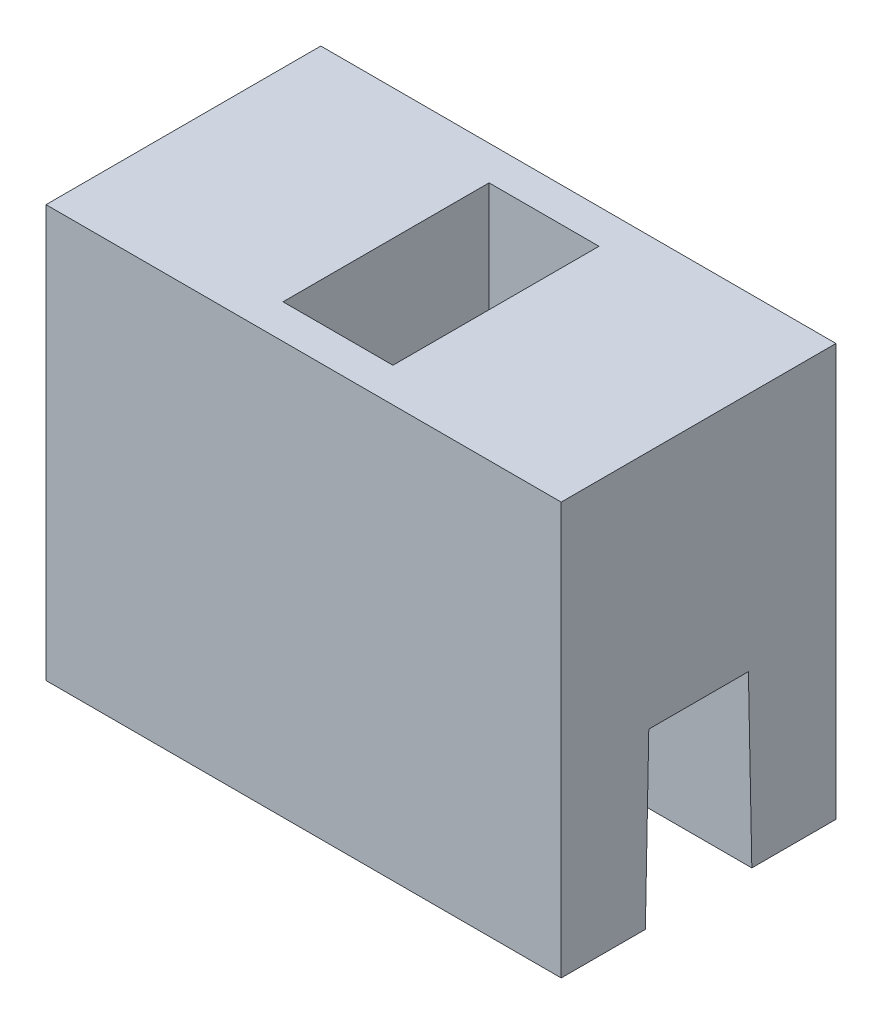
SolidWorks part; units mm, degrees
ref_plane "Front Plane" through (0, 0, 0) normal (0, 0, 1) x (1, 0, 0)
ref_plane "Top Plane" through (0, 0, 0) normal (0, 1, 0) x (1, 0, 0)
ref_plane "Right Plane" through (0, 0, 0) normal (1, 0, 0) x (0, 0, -1)
sketch "Sketch1" plane through (0, 0, 0) normal (1, 0, 0) x (0, 0, -1)
  line L0 (-1.55, 0) -> (-1.45, 5)
  line L1 (-1.45, 5) -> (1.45, 5)
  line L2 (1.45, 5) -> (1.55, 0)
  line L3 (1.55, 0) -> (4, 0)
  line L4 (4, 0) -> (4, 12)
  line L5 (4, 12) -> (-4, 12)
  line L6 (-4, 12) -> (-4, 0)
  line L7 (-4, 0) -> (-1.55, 0)
  point P9 (0, 5)
  point P10 (0, 12)
  dimension "D1" = 0.1
  dimension "D2" = 3.1
  dimension "D3" = 8
  dimension "D4" = 7
  dimension "D5" = 5
extrude "Boss-Extrude1" add sketch "Sketch1" along normal mid plane 15
sketch "Sketch2" plane through (0, 12, 0) normal (0, 1, 0) x (1, 0, 0)
  line L0 (7.5, 4) -> (-7.5, 4) construction
  line L1 (1.6, 3) -> (-1.6, 3)
  line L2 (1.6, 3) -> (1.6, -3)
  line L3 (1.6, -3) -> (-1.6, -3)
  line L4 (-1.6, 3) -> (-1.6, -3)
  point P4 (0, 3)
  point P5 (1.6, 0)
  dimension "D1" = 3.2
  dimension "D2" = 1
extrude "Cut-Extrude1" cut sketch "Sketch2" against normal blind 5
fillet "Fillet1" radius 1.5 2 edges at (-1.6, 7, 0) (1.6, 7, 0)
